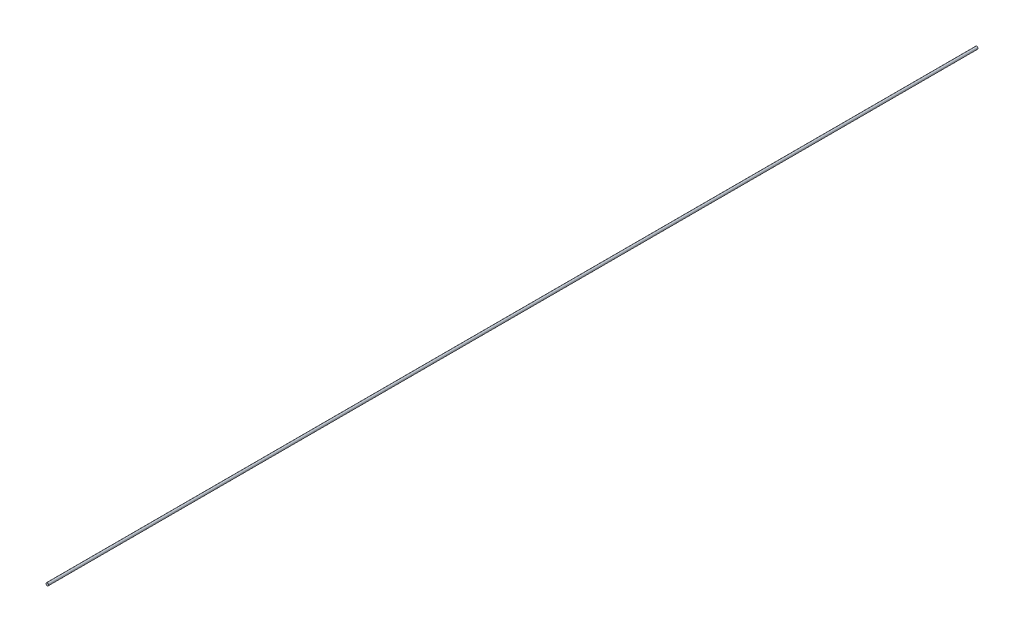
SolidWorks part; units mm, degrees
ref_plane "Plan de face" through (0, 0, 0) normal (0, 0, 1) x (1, 0, 0)
ref_plane "Plan de dessus" through (0, 0, 0) normal (0, 1, 0) x (1, 0, 0)
ref_plane "Plan de droite" through (0, 0, 0) normal (1, 0, 0) x (0, 0, -1)
sketch "Esquisse1" plane through (0, 0, 0) normal (0, 0, 1) x (1, 0, 0)
  circle A0 centre (0, 0) radius 1.5
  dimension "D1" = 3
extrude "Boss.-Extru.1" add sketch "Esquisse1" along normal blind 1088.1
